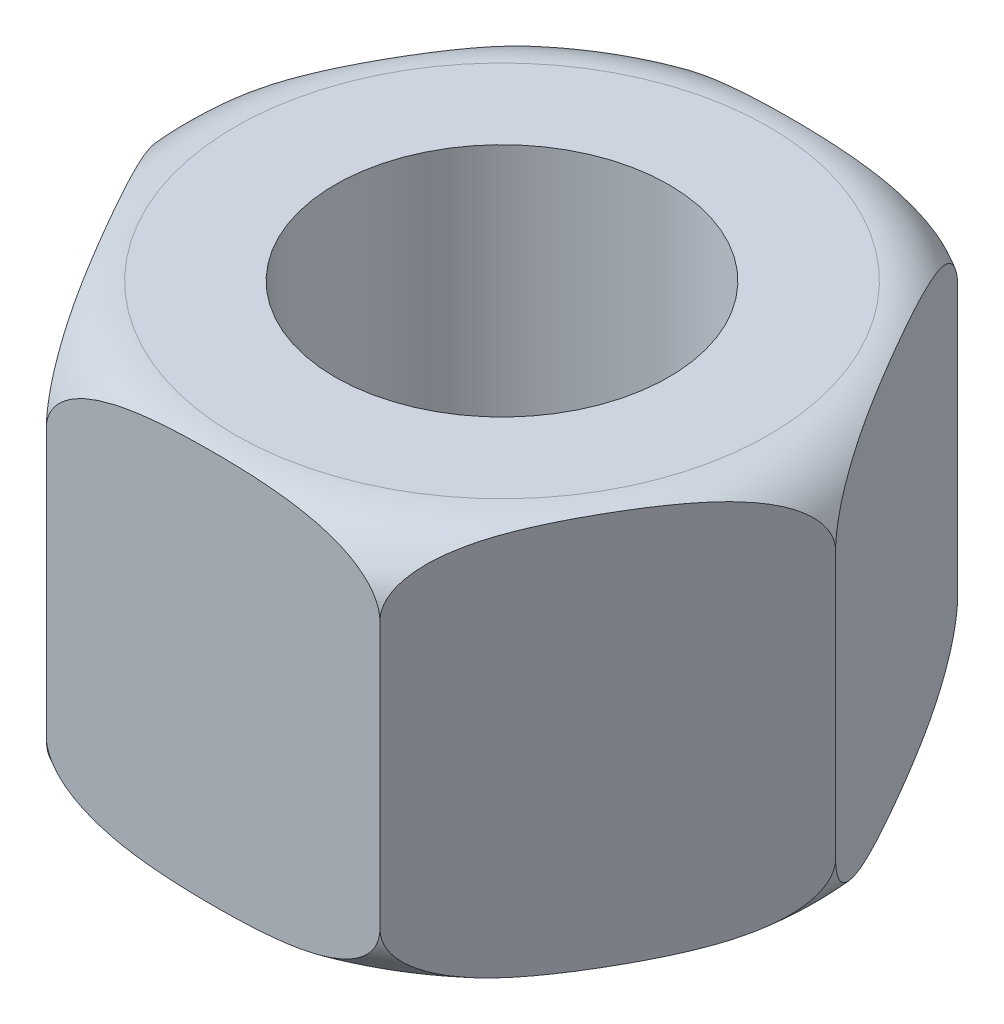
SolidWorks part; units mm, degrees
ref_plane "Front Plane" through (0, 0, 0) normal (0, 0, 1) x (1, 0, 0)
ref_plane "Top Plane" through (0, 0, 0) normal (0, 1, 0) x (1, 0, 0)
ref_plane "Right Plane" through (0, 0, 0) normal (1, 0, 0) x (0, 0, -1)
sketch "Sketch1" plane through (0, 0, 0) normal (0, 1, 0) x (1, 0, 0)
  line L1 (2.5, 0) -> (1.25, 2.1651)
  line L2 (1.25, 2.1651) -> (-1.25, 2.1651)
  line L3 (-1.25, 2.1651) -> (-2.5, 0)
  line L4 (-2.5, 0) -> (-1.25, -2.1651)
  line L5 (-1.25, -2.1651) -> (1.25, -2.1651)
  line L6 (1.25, -2.1651) -> (2.5, 0)
  dimension "D1" = 5
extrude "Boss-Extrude1" add sketch "Sketch1" along normal mid plane 3
sketch "Sketch2" plane through (0, 1.5, 0) normal (0, 1, 0) x (1, 0, 0)
  circle A0 centre (0, 0) radius 1.25
extrude "Cut-Extrude1" cut sketch "Sketch2" against normal through all
sketch "Sketch3" plane through (0, 0, 0) normal (0, 0, 1) x (1, 0, 0)
  line L0 (-2, 1.5) -> (-1.792, 1.5)
  line L1 (-2.5, -1) -> (-2.5, -0.7132)
  line L2 (-2.5, 1) -> (-2.5, 0.8706)
  line L3 (-2.5, 1.5) -> (-1.25, 1.5) construction
  line L4 (-1.792, 1.5) -> (-2.4543, 1.8689)
  line L6 (-2.4543, 1.8689) -> (-2.8723, 1.2664)
  line L7 (-2.8723, 1.2664) -> (-2.5, 0.8706)
  line L9 (-2.5, 1.5) -> (-2.5, -1.5) construction
  line L11 (-2, -1.5) -> (-1.8592, -1.5)
  line L12 (-2.5, -1.5) -> (-1.25, -1.5) construction
  line L13 (0, 0) -> (0, 1.832) construction
  line L14 (-1.8592, -1.5) -> (-2.4543, -1.8396)
  line L15 (-2.4543, -1.8396) -> (-2.9927, -1.5)
  line L16 (-2.9927, -1.5) -> (-2.5, -0.7132)
  line L17 (-2.5, -0.7132) -> (-2.5, -1.5)
  arc A0 (-2, 1.5) -> (-2.5, 1) centre (-2, 1) ccw
  arc A1 (-2, -1.5) -> (-2.5, -1) centre (-2, -1) cw
  point P17 (-2.5, 1.5)
  dimension "D1" = 0.5
revolve "Cut-Revolve1" cut sketch "Sketch3" angle 360 about L13
